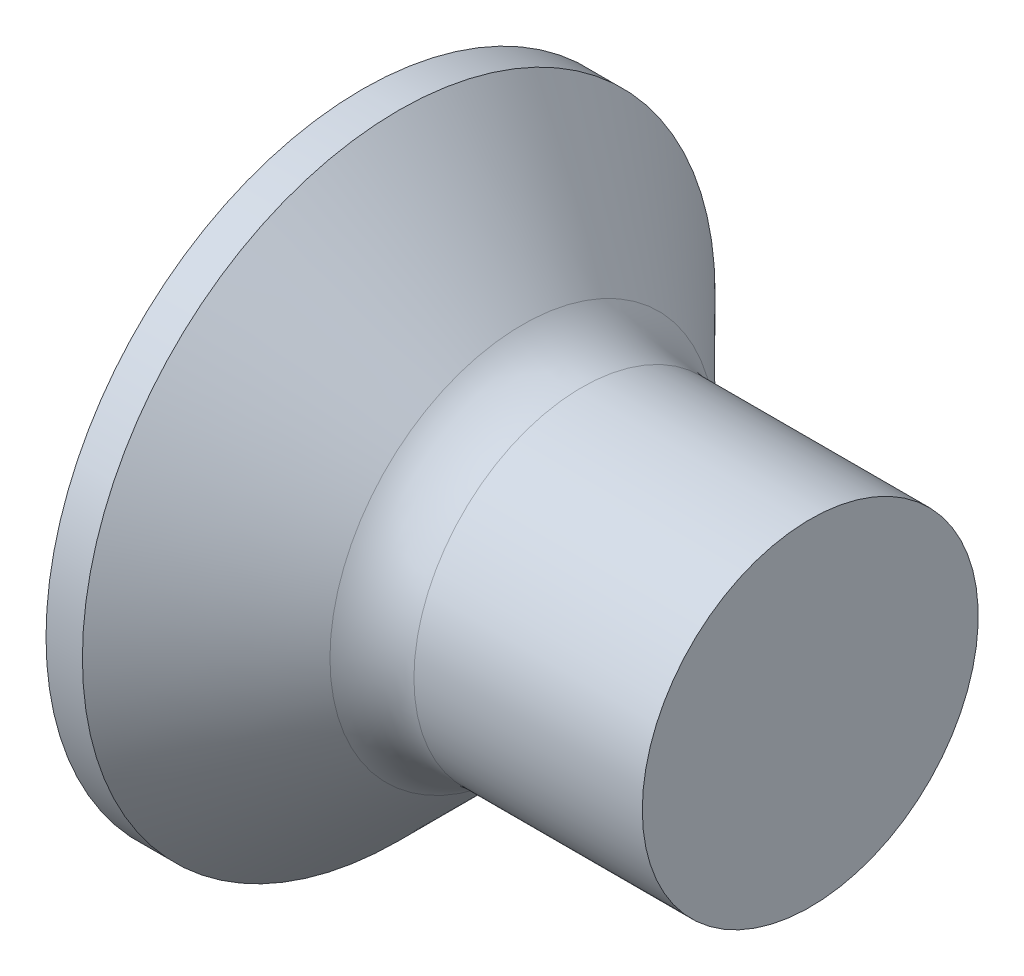
SolidWorks part; units mm, degrees
revolve "Base-Revolve" add sketch "BodySke"
sketch "BodySke" plane through (0, 0, 0) normal (0, 0, 1) x (1, 0, 0)
  line L0 (0, 0) -> (0, 5.65)
  line L1 (0, 5.65) -> (0.65, 5.65)
  line L2 (3.3, 3) -> (8, 3)
  line L3 (8, 3) -> (8, 0)
  line L4 (8, 0) -> (0, 0)
  line L5 (-6.35, 0) -> (82.55, 0) construction
  line L6 (3.3, -3) -> (8, -3) construction
  line L7 (0.65, -5.65) -> (3.3, -3) construction
  line L8 (0.65, 5.65) -> (3.3, 3)
  line L9 (0, -5.65) -> (0.65, -5.65) construction
  line L10 (4.3, 4.5875) -> (4.3, -4.9375) construction
  line L11 (0, 6.35) -> (0, -3.175) construction
  dimension "Diameter" = 6
  dimension "Length" = 8
  dimension "Head_ht" = 3.3
  dimension "Head_dia" = 11.3
  dimension "Head_ang" = 90
  dimension "D6" = 0.65
  dimension "Advance" = 1
  dimension "Thread_nom" = 8
cosmetic thread "ThreadCosmetic" [suppressed]
fillet "Fillet1" radius 1.5 1 edges at (3.3, 0, 3)
material "Plastique personnalisé"
ref_plane "Plane1" through (0, 0, 0) normal (0, 0, 1) x (1, 0, 0)
ref_plane "Plane2" through (0, 0, 0) normal (0, 1, 0) x (1, 0, 0)
ref_plane "Plane3" through (0, 0, 0) normal (1, 0, 0) x (0, 0, -1)
sketch "Sketch3" plane through (0, 0, 0) normal (-1, 0, 0) x (0, 0, 1)
  line L0 (-0.71, 3.3) -> (0.71, 3.3)
  line L1 (0.71, 3.3) -> (0.71, -3.3)
  line L2 (0.71, -3.3) -> (-0.71, -3.3)
  line L3 (-0.71, -3.3) -> (-0.71, 3.3)
  dimension "Cross_dia" = 6.6
  dimension "Cross_width" = 1.42
  dimension "D1" = 3.3
  dimension "D2" = 0.71
ref_plane "Plane4" through (3.45, 0, 0) normal (-1, 0, 0) x (0, 0, 1)
sketch "Sketch4" plane through (3.45, 0, 0) normal (-1, 0, 0) x (0, 0, 1)
  line L0 (-0.71, 1.5799) -> (0.71, 1.5799)
  line L3 (0.71, 1.5799) -> (0.71, -1.5799)
  line L4 (0.71, -1.5799) -> (-0.71, -1.5799)
  line L5 (-0.71, -1.5799) -> (-0.71, 1.5799)
  dimension "D2" = 3.1598
  dimension "D1" = 1.42
  dimension "D4" = 1.5799
  dimension "D3" = 0.71
loft "Recess" cut profiles "Sketch3", "Sketch4"
pattern_circular "RecPat" count 2 every 90 about axis through (0, 0, 0) along (1, 0, 0) of "Recess"
sketch "RecCorSke" plane through (0, 0, 0) normal (0, 0, 1) x (1, 0, 0)
  line L0 (-3.175, 0) -> (15.875, 0) construction
  line L2 (0, 0) -> (0, 1.5217)
  line L3 (0, 1.5217) -> (3.45, 1.2805)
  line L4 (3.45, 1.2805) -> (3.8661, 0)
  line L5 (3.8661, 0) -> (0, 0)
  dimension "Diameter" = 2.561
  dimension "Depth" = 3.45
  dimension "Draft_angle" = 4
  dimension "Bottom_angle" = 18
revolve "RecessCore" cut sketch "RecCorSke" angle 360 about L0
sketch "ThdSchSke" plane through (0, 0, 0) normal (0, 0, 1) x (1, 0, 0)
  line L0 (4.3, -2.4455) -> (3.9117, -3)
  line L1 (4.3, -2.4455) -> (4.6883, -3)
  line L2 (4.6883, -3) -> (4.6883, -3.75)
  line L3 (-3.175, 0) -> (5.1513, 0) construction
  line L5 (4.6883, -3.75) -> (3.9117, -3.75)
  line L6 (3.9117, -3.75) -> (3.9117, -3)
  line L7 (0, 5.65) -> (0, -5.65) construction
  dimension "Diameter" = 6
  dimension "Thread_minor" = 4.891
  dimension "Start" = 4.3
revolve "ThreadSchematic" [suppressed] cut sketch "ThdSchSke" angle 360 about L3
pattern_linear "ThdSchPat" [suppressed]
equation "\"D1@Sketch3\" = \"Cross_dia@Sketch3\" / 2"
equation "\"D2@Sketch3\" = \"Cross_width@Sketch3\" / 2"
equation "\"Depth@RecCorSke\" = \"Cross_depth@Plane4\""
equation "\"D1@Sketch4\" = \"Cross_width@Sketch3\""
equation "\"D2@Sketch4\" = \"Cross_dia@Sketch3\" - 2.0 * \"Cross_depth@Plane4\" * tan(26.5  * 0.017453292)"
equation "\"D3@Sketch4\" = \"D1@Sketch4\" / 2"
equation "\"D4@Sketch4\" = \"D2@Sketch4\" / 2"
equation "\"Thread_length@ThreadCosmetic\" = ((sgn( (\"Length@BodySke\" - \"Advance@BodySke\" * 1.0 - \"Head_ht@BodySke\" ) - \"Thread_nom@BodySke\" )-1)*( (\"Length@BodySke\" - \"Advance@BodySke\" * 1.0 - \"Head_ht@BodySke\" ) - \"Thread_nom@BodySke\" ))/-2+ \"Thread_nom@BodySke\""
equation "\"Thread_minor@ThdSchSke\" = \"Thread_minor@ThreadCosmetic\""
equation "\"Diameter@ThdSchSke\" = \"Diameter@BodySke\""
equation "\"Overcut@ThdSchSke\" = \"Diameter@BodySke\" * 1.25"
equation "\"Start@ThdSchSke\" = 0.000001 + \"Length@BodySke\" - \"Thread_length@ThreadCosmetic\"  '---Countersunk---"
equation "\"Num_threads@ThdSchPat\" = int( \"Thread_length@ThreadCosmetic\" / \"Advance@BodySke\" + 0.999 )  + 1"
equation "\"Advance@ThdSchPat\" = \"Thread_length@ThreadCosmetic\" /  (\"Num_threads@ThdSchPat\" - 1) 'relax it"
